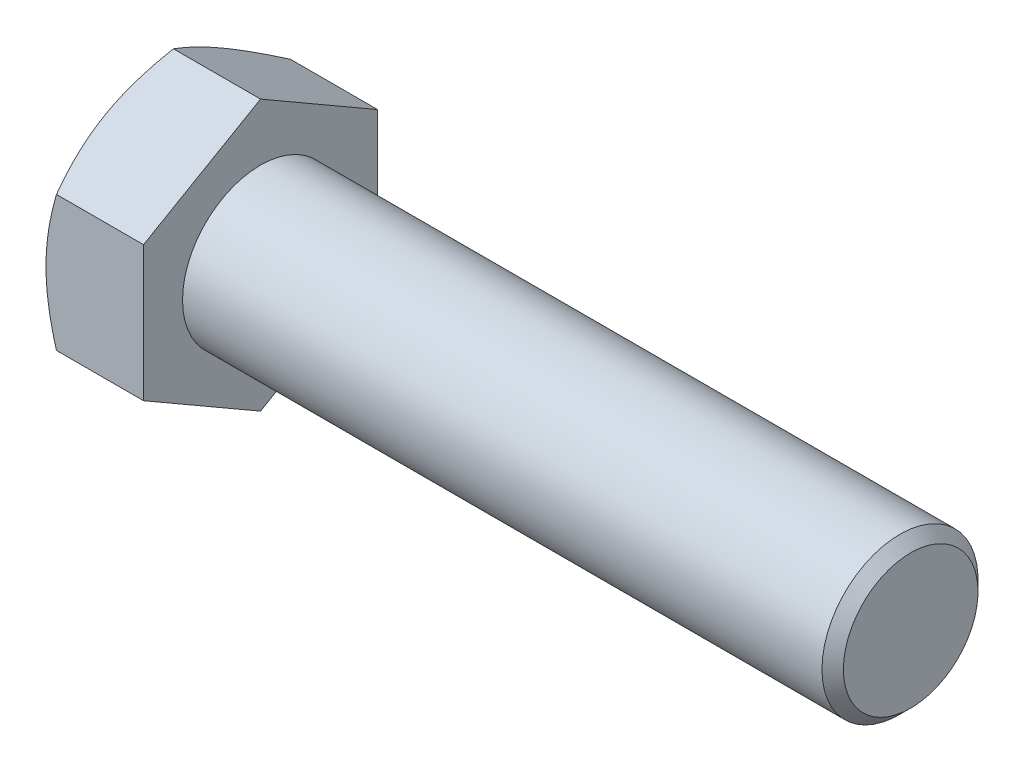
SolidWorks part; units mm, degrees
extrude "BaseHead" add sketch "Sketch1" along normal blind 15
sketch "Sketch1" plane through (0, 0, 0) normal (1, 0, 0) x (0, 0, -1)
  line L0 (18, 10.3923) -> (18, -10.3923)
  line L1 (-18, 10.3923) -> (-18, -10.3923)
  line L2 (18, -10.3923) -> (0, -20.7846)
  line L3 (0, -20.7846) -> (-18, -10.3923)
  line L4 (18, 10.3923) -> (0, 20.7846)
  line L5 (0, 20.7846) -> (-18, 10.3923)
  dimension "D2" = 120
ref_plane "Plane1" through (0, 0, 0) normal (0, 0, 1) x (1, 0, 0)
ref_plane "Plane2" through (0, 0, 0) normal (0, 1, 0) x (1, 0, 0)
ref_plane "Plane3" through (0, 0, 0) normal (1, 0, 0) x (0, 0, -1)
sketch "BodySke" plane through (0, 0, 0) normal (0, 0, 1) x (1, 0, 0)
  line L0 (0, 10.3923) -> (0, -10.3923) construction
  line L1 (0, 0) -> (115, 0)
  line L2 (0, 0) -> (0, 12)
  line L3 (0, 12) -> (113.352, 12)
  line L4 (115, 0) -> (115, 10.352)
  line L5 (15, 20.7846) -> (15, 10.3923) construction
  line L6 (115, 10.352) -> (113.352, 12)
  line L7 (0, 0) -> (96.52, 0) construction
  line L8 (115, -10.352) -> (113.352, -12) construction
  line L9 (0, -12) -> (113.352, -12) construction
  line L10 (18, 15.24) -> (18, -1.27) construction
  line L11 (61, 15.24) -> (61, -1.27) construction
  line L12 (15, 10.3923) -> (15, -10.3923) construction
revolve "BaseBody" add sketch "BodySke"
cosmetic thread "ThreadCosmetic" [suppressed]
fillet "HeadFillet" [suppressed] radius 0.8
sketch "Sketch3" plane through (0, 0, 0) normal (0, 0, 1) x (1, 0, 0)
  line L0 (0, 18) -> (4.4944, 25.7846)
  line L1 (0, 20.7846) -> (0, 10.3923) construction
  line L2 (4.4944, 25.7846) -> (4.4944, 30.7846)
  line L3 (4.4944, 30.7846) -> (-10, 30.7846)
  line L4 (-10, 30.7846) -> (-10, 18)
  line L5 (-10, 18) -> (0, 18)
  line L6 (0, 0) -> (99.06, 0) construction
  line L7 (15, 20.7846) -> (0, 20.7846) construction
  dimension "D2" = 5
  dimension "D3" = 10
  dimension "D4" = 5
  dimension "Head_ch_ang" = 30
revolve "HeadChamfer" cut sketch "Sketch3" angle 360 about L6
sketch "ThdSchSke" plane through (0, 0, 0) normal (0, 0, 1) x (1, 0, 0)
  line L0 (61, -10.352) -> (59.8461, -12)
  line L1 (61, -10.352) -> (62.1539, -12)
  line L2 (62.1539, -12) -> (62.1539, -15)
  line L3 (-3.175, 0) -> (5.1513, 0) construction
  line L5 (62.1539, -15) -> (59.8461, -15)
  line L6 (59.8461, -15) -> (59.8461, -12)
revolve "ThreadSchematic" [suppressed] cut sketch "ThdSchSke" angle 360 about L3
pattern_linear "ThdSchPat" [suppressed]
equation "\"D3@Sketch1\" = \"Width_flats@Sketch1\" / 2"
equation "\"D4@Sketch1\" = \"D3@Sketch1\""
equation "\"D5@Sketch1\" = \"D4@Sketch1\""
equation "\"Thread_minor@ThreadCosmetic\" = \"Minor_dia@BodySke\""
equation "\"D1@Sketch3\" = \"Width_flats@Sketch1\" / 2"
equation "' \"D1@Sketch4\" = \"Width_flats@Sketch1\""
equation "\"Thread_length@ThreadCosmetic\" = ((sgn( (\"Length@BodySke\" - \"Advance@BodySke\" ) - \"Thread_nom@BodySke\" )-1)*( (\"Length@BodySke\" - \"Advance@BodySke\" ) - \"Thread_nom@BodySke\" ))/-2+ \"Thread_nom@BodySke\""
equation "\"Thread_minor@ThdSchSke\" = \"Minor_dia@BodySke\""
equation "\"Diameter@ThdSchSke\" = \"Diameter@BodySke\""
equation "\"Overcut@ThdSchSke\" = \"Diameter@BodySke\" * 1.25"
equation "\"Start@ThdSchSke\" = \"Head_ht@BaseHead\" + \"Length@BodySke\" - \"Thread_length@ThreadCosmetic\"  '---Non-countersunk---"
equation "\"Num_threads@ThdSchPat\" = int( \"Thread_length@ThreadCosmetic\" / \"Advance@BodySke\" + 0.999 )  + 1"
equation "\"Advance@ThdSchPat\" = \"Thread_length@ThreadCosmetic\" /  (\"Num_threads@ThdSchPat\" - 1) 'relax it"
equation "\"Num_threads@ThdSchPat\" = \"Num_threads@ThdSchPat\" - sgn( \"Num_threads@ThdSchPat\" - 1) '---chamfered tips only---"
